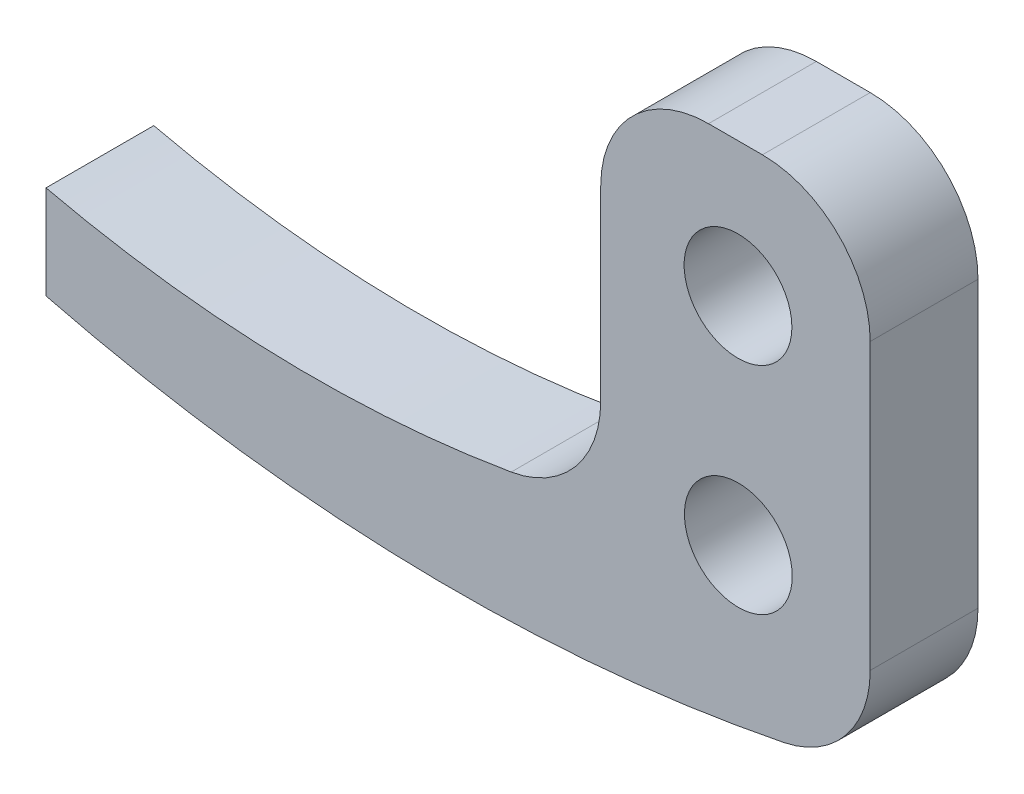
SolidWorks part; units mm, degrees
ref_plane "Front Plane" through (0, 0, 0) normal (0, 0, 1) x (1, 0, 0)
ref_plane "Top Plane" through (0, 0, 0) normal (0, 1, 0) x (1, 0, 0)
ref_plane "Right Plane" through (0, 0, 0) normal (1, 0, 0) x (0, 0, -1)
sketch "Sketch2" plane through (0, 0, 0) normal (0, 0, 1) x (1, 0, 0)
  line L0 (0, 13.0013) -> (0, 0) construction
  line L1 (-1, 8) -> (-1, 5) construction
  line L6 (-1, 8) -> (-2, 8) construction
  line L7 (-2, 8) -> (-2, 5) construction
  line L8 (-2, 5) -> (-1, 5) construction
  line L9 (9, 22.6262) -> (9.0232, 8.3763) construction
  line L10 (3, 14.8726) -> (3, -4.3572) construction
  line L11 (9.0232, 8.3763) -> (9.0361, 0.4748) construction
  line L12 (-3.8232, 5.9572) -> (-3.8232, 7.6948)
  line L13 (6.4698, 7.7965) -> (6.4698, 14.8726)
  line L14 (6.4698, 14.8726) -> (11.4698, 14.8726)
  line L15 (11.4698, 14.8726) -> (11.4698, 9.7431)
  line L16 (11.4698, 9.7431) -> (11.4698, 5.9936)
  circle A8 centre (9.0232, 8.3763) radius 1
  circle A9 centre (9.0167, 12.3762) radius 1
  arc A12 (-3.8232, 5.9572) -> (11.4698, 5.9936) centre (3.7518, 36.0434) ccw
  arc A13 (-3.8232, 7.6948) -> (6.4698, 7.7965) centre (1.1139, 28.9484) ccw
  point P16 (9, 22.6262)
  dimension "D1" = 1
  dimension "D4" = 4
  dimension "D7" = 2
  dimension "D2" = 3
  dimension "D3" = 1
  dimension "D5" = 9
  dimension "D6" = 8
  dimension "D8" = 3
  dimension "D9" = 10.25
  dimension "D10" = 5
extrude "Boss-Extrude2" add sketch "Sketch2" along normal blind 2
fillet "Fillet1" radius 2 4 edges at (6.4698, 7.7965, 1) (11.4698, 5.9936, 1) (6.4698, 14.8726, 1) (11.4698, 14.8726, 1)
